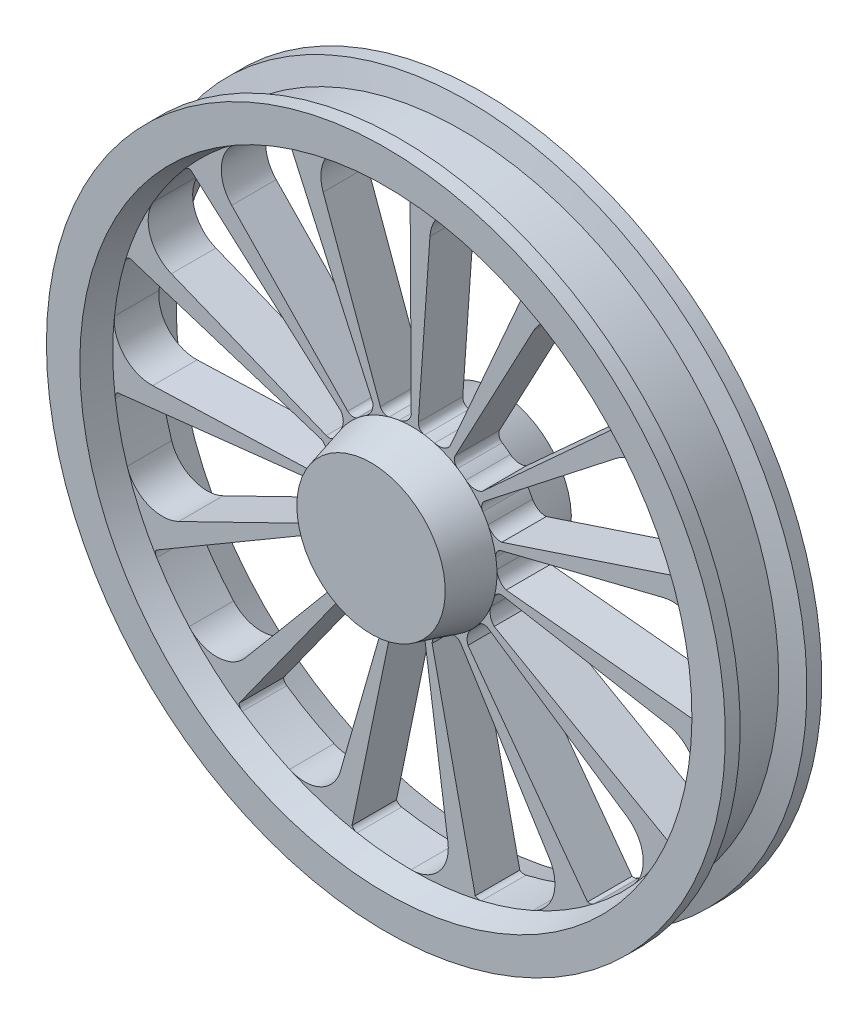
SolidWorks part; units mm, degrees
material "1060 Alloy"
ref_plane "Front Plane" through (0, 0, 0) normal (0, 0, 1) x (1, 0, 0)
ref_plane "Top Plane" through (0, 0, 0) normal (0, 1, 0) x (1, 0, 0)
ref_plane "Right Plane" through (0, 0, 0) normal (1, 0, 0) x (0, 0, -1)
sketch "Sketch3" plane through (0, 0, 0) normal (1, 0, 0) x (0, 0, -1)
  line L1 (-85, -159.784) -> (-85, -259.784)
  line L2 (-36.9615, 167.716) -> (36.9615, 167.716)
  line L3 (36.9615, 167.716) -> (45, 197.716)
  line L4 (45, 197.716) -> (65, 197.716)
  line L5 (65, 197.716) -> (65, 152.716)
  line L6 (65, 152.716) -> (30, 143.3378)
  line L7 (30, 143.3378) -> (30, -145.0468)
  line L8 (30, -145.0468) -> (85, -159.784)
  line L9 (85, -159.784) -> (85, -259.784)
  line L10 (85, -259.784) -> (-85, -259.784)
  line L11 (-30, -145.0468) -> (-85, -159.784)
  line L12 (-30, 143.3378) -> (-30, -145.0468)
  line L13 (-65, 152.716) -> (-30, 143.3378)
  line L14 (-65, 197.716) -> (-65, 152.716)
  line L15 (-45, 197.716) -> (-65, 197.716)
  line L16 (-36.9615, 167.716) -> (-45, 197.716)
  point P4 (0, 0)
  point P8 (0, 0)
  point P36 (0, 167.716)
  dimension "D1" = 130
  dimension "D2" = 45
  dimension "D3" = 30
revolve "Revolve1" add sketch "Sketch3" angle 360 about L10
sketch "Sketch4" plane through (0, 0, -30) normal (0, 0, -1) x (-1, 0, 0)
  line L0 (0, 133.2106) -> (0, -126.5394)
  line L1 (42.5253, -142.9466) -> (119.5579, 68.6987)
  line L2 (52.6577, -143.4341) -> (166.2146, 107.476)
  line L3 (159.8453, 99.2344) -> (54.1954, -138.059)
  line L4 (86.3708, -170.3444) -> (242.8276, -8.3287)
  line L5 (95.429, -174.9108) -> (301.2227, 8.1191)
  line L6 (292.0519, 3.1807) -> (99.02, -170.626)
  line L7 (115.2821, -213.207) -> (324.1101, -128.835)
  line L8 (121.6997, -221.063) -> (384.1466, -137.5606)
  line L9 (373.76, -138.342) -> (126.7231, -218.6092)
  line L10 (124.26, -264.1232) -> (349.3511, -271.9836)
  line L11 (126.9275, -273.9103) -> (400.6481, -304.3739)
  line L12 (390.8417, -300.8631) -> (132.5146, -273.7118)
  line L13 (111.7522, -314.2892) -> (314.186, -413.0228)
  line L14 (110.2083, -324.3151) -> (347.8739, -463.4771)
  line L15 (340.3433, -456.2813) -> (115.3932, -326.4063)
  line L16 (79.9215, -355.0307) -> (224.6954, -527.5656)
  line L17 (74.4332, -363.5618) -> (234.9492, -587.36)
  line L18 (230.9964, -577.7233) -> (78.3192, -367.5811)
  line L19 (34.2716, -379.3032) -> (96.3529, -595.8065)
  line L20 (25.7878, -384.8645) -> (81.3996, -654.602)
  line L21 (81.7082, -644.1907) -> (27.7031, -390.1168)
  line L22 (-17.3042, -382.9097) -> (-48.6499, -605.9461)
  line L23 (-27.3165, -384.5395) -> (-86.2247, -653.5764)
  line L24 (-81.7082, -644.1907) -> (-27.7031, -390.1168)
  line L25 (-65.8879, -365.2267) -> (-185.2407, -556.2311)
  line L26 (-75.6975, -362.6433) -> (-238.94, -584.4605)
  line L27 (-230.9964, -577.7233) -> (-78.3192, -367.5811)
  line L28 (-103.079, -329.3116) -> (-289.8017, -455.2577)
  line L29 (-110.9897, -322.9617) -> (-350.3404, -459.2051)
  line L30 (-340.3433, -456.2813) -> (-115.3932, -326.4063)
  line L31 (-122.4468, -281.3747) -> (-344.2533, -320.4851)
  line L32 (-127.0908, -272.3561) -> (-401.1637, -299.4679)
  line L33 (-390.8417, -300.8631) -> (-132.5146, -273.7118)
  line L34 (-120.6424, -229.7045) -> (-339.1805, -175.2168)
  line L35 (-121.2168, -219.5767) -> (-382.6222, -132.8691)
  line L36 (-373.76, -138.342) -> (-126.7231, -218.6092)
  line L37 (-97.9779, -183.2353) -> (-275.4602, -44.5709)
  line L38 (-94.3832, -173.7495) -> (-297.9219, 11.785)
  line L39 (-292.0519, 3.1807) -> (-99.02, -170.626)
  line L40 (-58.3721, -150.0021) -> (-164.1104, 48.8627)
  line L41 (-51.23, -142.7984) -> (-161.7081, 109.4824)
  line L42 (-159.8453, 99.2344) -> (-54.1954, -138.059)
  line L43 (-8.6732, -135.7512) -> (-24.3844, 88.9285)
  line L44 (0.7814, -132.0752) -> (2.4665, 143.3302)
  arc A0 (236.1508, 66.9268) -> (173.2792, 104.1961) centre (0, -259.784) ccw
  circle A1 centre (0, -259.784) radius 114.7372 construction
  circle A2 centre (0, -259.784) radius 403.1218 construction
  arc A3 (30.4725, -149.1673) -> (17.0313, -146.3179) centre (0, -259.784) ccw
  arc A4 (82.8493, 134.7324) -> (10.2544, 143.2073) centre (0, -259.784) ccw
  arc A5 (17.0313, -146.3179) -> (0, -126.5394) centre (20, -126.5394) cw
  arc A6 (30.4725, -149.1673) -> (42.5253, -142.9466) centre (33.1284, -139.5264) ccw
  arc A7 (10.2544, 143.2073) -> (0, 133.2106) centre (10, 133.2106) ccw
  arc A8 (82.8493, 134.7324) -> (119.5579, 68.6987) centre (72.5733, 85.7997) cw
  arc A9 (173.2792, 104.1961) -> (159.8453, 99.2344) centre (168.9807, 95.167) ccw
  arc A10 (236.1508, 66.9268) -> (242.8276, -8.3287) centre (206.8606, 26.4042) cw
  arc A11 (72.8299, -171.1249) -> (86.3708, -170.3444) centre (79.1774, -163.3978) ccw
  arc A12 (61.7097, -163.0548) -> (54.1954, -138.059) centre (72.4664, -146.1938) cw
  arc A13 (72.8299, -171.1249) -> (61.7097, -163.0548) centre (0, -259.784) ccw
  arc A14 (348.6198, -57.37) -> (306.3424, 2.2494) centre (0, -259.784) ccw
  arc A15 (306.3424, 2.2494) -> (292.0519, 3.1807) centre (298.7432, -4.2507) ccw
  arc A16 (348.6198, -57.37) -> (324.1101, -128.835) centre (305.3798, -82.4758) cw
  arc A17 (102.5943, -208.4125) -> (115.2821, -213.207) centre (111.536, -203.9352) ccw
  arc A18 (95.7179, -196.517) -> (99.02, -170.626) centre (112.4026, -185.4889) cw
  arc A19 (102.5943, -208.4125) -> (95.7179, -196.517) centre (0, -259.784) ccw
  arc A20 (400.8092, -216.6661) -> (386.4363, -145.0053) centre (0, -259.784) ccw
  arc A21 (386.4363, -145.0053) -> (373.76, -138.342) centre (376.8502, -147.8526) ccw
  arc A22 (400.8092, -216.6661) -> (349.3511, -271.9836) centre (351.096, -222.0141) cw
  arc A23 (114.6193, -254.5827) -> (124.26, -264.1232) centre (124.609, -254.1293) ccw
  arc A24 (113.1757, -240.9187) -> (126.7231, -218.6092) centre (132.9035, -237.6303) cw
  arc A25 (114.6193, -254.5827) -> (113.1757, -240.9187) centre (0, -259.784) ccw
  arc A26 (383.6951, -383.4176) -> (399.7118, -312.1063) centre (0, -259.784) ccw
  arc A27 (399.7118, -312.1063) -> (390.8417, -300.8631) centre (389.7964, -310.8083) ccw
  arc A28 (383.6951, -383.4176) -> (314.186, -413.0228) centre (336.1046, -368.0831) cw
  arc A29 (106.8255, -301.6522) -> (111.7522, -314.2892) centre (116.1359, -305.3012) ccw
  arc A30 (111.0643, -288.5824) -> (132.5146, -273.7118) centre (130.4241, -293.6023) cw
  arc A31 (106.8255, -301.6522) -> (111.0643, -288.5824) centre (0, -259.784) ccw
  arc A32 (300.2366, -528.7917) -> (343.8735, -470.1602) centre (0, -259.784) ccw
  arc A33 (343.8735, -470.1602) -> (340.3433, -456.2813) centre (335.3433, -464.9415) ccw
  arc A34 (300.2366, -528.7917) -> (224.6954, -527.5656) centre (262.9976, -495.4262) cw
  arc A35 (80.5606, -341.4823) -> (79.9215, -355.0307) centre (87.5819, -348.6028) ccw
  arc A36 (89.7489, -331.2666) -> (115.3932, -326.4063) centre (105.3932, -343.7268) cw
  arc A37 (80.5606, -341.4823) -> (89.7489, -331.2666) centre (0, -259.784) ccw
  arc A38 (164.8644, -627.652) -> (228.5764, -591.8382) centre (0, -259.784) ccw
  arc A39 (228.5764, -591.8382) -> (230.9964, -577.7233) centre (222.9062, -583.6011) ccw
  arc A40 (164.8644, -627.652) -> (96.3529, -595.8065) centre (144.416, -582.0246) cw
  arc A41 (40.3661, -367.1861) -> (34.2716, -379.3032) centre (43.8842, -376.5468) ccw
  arc A42 (52.9151, -361.5907) -> (78.3192, -367.5811) centre (62.1389, -379.3368) cw
  arc A43 (40.3661, -367.1861) -> (52.9151, -361.5907) centre (0, -259.784) ccw
  arc A44 (0.9858, -662.9046) -> (73.7563, -656.101) centre (0, -259.784) ccw
  arc A45 (73.7563, -656.101) -> (81.7082, -644.1907) centre (71.9267, -646.2698) ccw
  arc A46 (0.9858, -662.9046) -> (-48.6499, -605.9461) centre (0.8635, -612.9047) cw
  arc A47 (-6.8081, -374.319) -> (-17.3042, -382.9097) centre (-7.4015, -384.3014) ccw
  arc A48 (6.9319, -374.3116) -> (27.7031, -390.1168) centre (8.1402, -394.2751) cw
  arc A49 (-6.8081, -374.319) -> (6.9319, -374.3116) centre (0, -259.784) ccw
  arc A50 (-163.0634, -628.4539) -> (-93.8169, -651.837) centre (0, -259.784) ccw
  arc A51 (-93.8169, -651.837) -> (-81.7082, -644.1907) centre (-91.4896, -642.1116) ccw
  arc A52 (-163.0634, -628.4539) -> (-185.2407, -556.2311) centre (-142.8383, -582.727) cw
  arc A53 (-52.8051, -361.6478) -> (-65.8879, -365.2267) centre (-57.4074, -370.5259) ccw
  arc A54 (-40.25, -367.2296) -> (-27.7031, -390.1168) centre (-47.2661, -385.9586) cw
  arc A55 (-52.8051, -361.6478) -> (-40.25, -367.2296) centre (0, -259.784) ccw
  arc A56 (-298.9174, -530.2569) -> (-245.1683, -579.7835) centre (0, -259.784) ccw
  arc A57 (-245.1683, -579.7835) -> (-230.9964, -577.7233) centre (-239.0866, -571.8454) ccw
  arc A58 (-298.9174, -530.2569) -> (-289.8017, -455.2577) centre (-261.842, -496.7096) cw
  arc A59 (-89.6717, -331.3635) -> (-103.079, -329.3116) centre (-97.4871, -337.602) ccw
  arc A60 (-80.4723, -341.5693) -> (-78.3192, -367.5811) centre (-94.4995, -355.8254) cw
  arc A61 (-89.6717, -331.3635) -> (-80.4723, -341.5693) centre (0, -259.784) ccw
  arc A62 (-383.0858, -385.2926) -> (-354.1279, -452.3991) centre (0, -259.784) ccw
  arc A63 (-354.1279, -452.3991) -> (-340.3433, -456.2813) centre (-345.3433, -447.621) ccw
  arc A64 (-383.0858, -385.2926) -> (-344.2533, -320.4851) centre (-335.5709, -369.7255) cw
  arc A65 (-111.0331, -288.7023) -> (-122.4468, -281.3747) centre (-120.7103, -291.2227) ccw
  arc A66 (-106.7802, -301.7676) -> (-115.3932, -326.4063) centre (-125.3932, -309.0858) cw
  arc A67 (-111.0331, -288.7023) -> (-106.7802, -301.7676) centre (0, -259.784) ccw
  arc A68 (-401.0153, -218.6268) -> (-401.8556, -291.7099) centre (0, -259.784) ccw
  arc A69 (-401.8556, -291.7099) -> (-390.8417, -300.8631) centre (-391.887, -290.9179) ccw
  arc A70 (-401.0153, -218.6268) -> (-339.1805, -175.2168) centre (-351.2766, -223.7316) cw
  arc A71 (-113.196, -241.041) -> (-120.6424, -229.7045) centre (-123.0616, -239.4074) ccw
  arc A72 (-114.6248, -254.7065) -> (-132.5146, -273.7118) centre (-134.6052, -253.8214) cw
  arc A73 (-113.196, -241.041) -> (-114.6248, -254.7065) centre (0, -259.784) ccw
  arc A74 (-349.6055, -59.0774) -> (-380.0988, -125.5003) centre (0, -259.784) ccw
  arc A75 (-380.0988, -125.5003) -> (-373.76, -138.342) centre (-370.6699, -128.8314) ccw
  arc A76 (-349.6055, -59.0774) -> (-275.4602, -44.5709) centre (-306.2433, -83.9714) cw
  arc A77 (-95.7862, -196.6205) -> (-97.9779, -183.2353) centre (-104.1345, -191.1154) ccw
  arc A78 (-102.6498, -208.5233) -> (-126.7231, -218.6092) centre (-120.5428, -199.588) cw
  arc A79 (-95.7862, -196.6205) -> (-102.6498, -208.5233) centre (0, -259.784) ccw
  arc A80 (-237.7458, 65.768) -> (-292.6194, 17.4903) centre (0, -259.784) ccw
  arc A81 (-292.6194, 17.4903) -> (-292.0519, 3.1807) centre (-285.3606, 10.6121) ccw
  arc A82 (-237.7458, 65.768) -> (-164.1104, 48.8627) centre (-208.2577, 25.3891) cw
  arc A83 (-61.8141, -163.1215) -> (-58.3721, -150.0021) centre (-67.2016, -154.6968) ccw
  arc A84 (-72.9256, -171.2036) -> (-99.02, -170.626) centre (-85.6374, -155.7631) cw
  arc A85 (-61.8141, -163.1215) -> (-72.9256, -171.2036) centre (0, -259.784) ccw
  arc A86 (-84.7777, 134.3225) -> (-154.5435, 112.5377) centre (0, -259.784) ccw
  arc A87 (-154.5435, 112.5377) -> (-159.8453, 99.2344) centre (-150.7098, 103.3018) ccw
  arc A88 (-84.7777, 134.3225) -> (-24.3844, 88.9285) centre (-74.2626, 85.4407) cw
  arc A89 (-17.1538, -146.3363) -> (-8.6732, -135.7512) centre (-18.6489, -136.4487) ccw
  arc A90 (-30.592, -149.2003) -> (-54.1954, -138.059) centre (-35.9245, -129.9243) cw
  arc A91 (-17.1538, -146.3363) -> (-30.592, -149.2003) centre (0, -259.784) ccw
  point P203 (0, -259.784)
  circle M1 centre (0, -259.784) radius 403.1218
  circle M2 centre (0, -259.784) radius 114.7372
  dimension "D2" = 20
  dimension "D3" = 10
  dimension "D4" = 10
  dimension "D5" = 50
  dimension "D1" = 20
  dimension "D6" = 4.351
  dimension "D7" = 15
extrude "Cut-Extrude1" cut sketch "Sketch4" against normal blind 100 contours A84 A83 L40 A82 A81 L38 M2 M1 | A78 A77 L37 A76 A75 L35 M2 M1 | A72 A71 L34 A70 A69 L32 M2 M1 | A66 A65 L31 A64 A63 L29 M2 M1 | A60 A59 L28 A58 A57 L26 M2 M1 | A54 A53 L25 A52 A51 L23 M2 M1 | A48 A47 L22 A46 A45 L20 M2 M1 | A42 A41 L19 A40 A39 L17 M2 M1 | A36 A35 L16 A34 A33 L14 M2 M1 | A30 A29 L13 A28 A27 L11 M2 M1 | A24 A23 L10 A22 A21 L8 M2 M1 | A18 A17 L7 A16 A15 L5 M2 M1 | A12 A11 L4 A10 A9 L2 M2 M1 | A8 A7 L44 A5 A6 L1 M1 M2 | A90 A89 L43 A88 A87 L41 M2 M1
